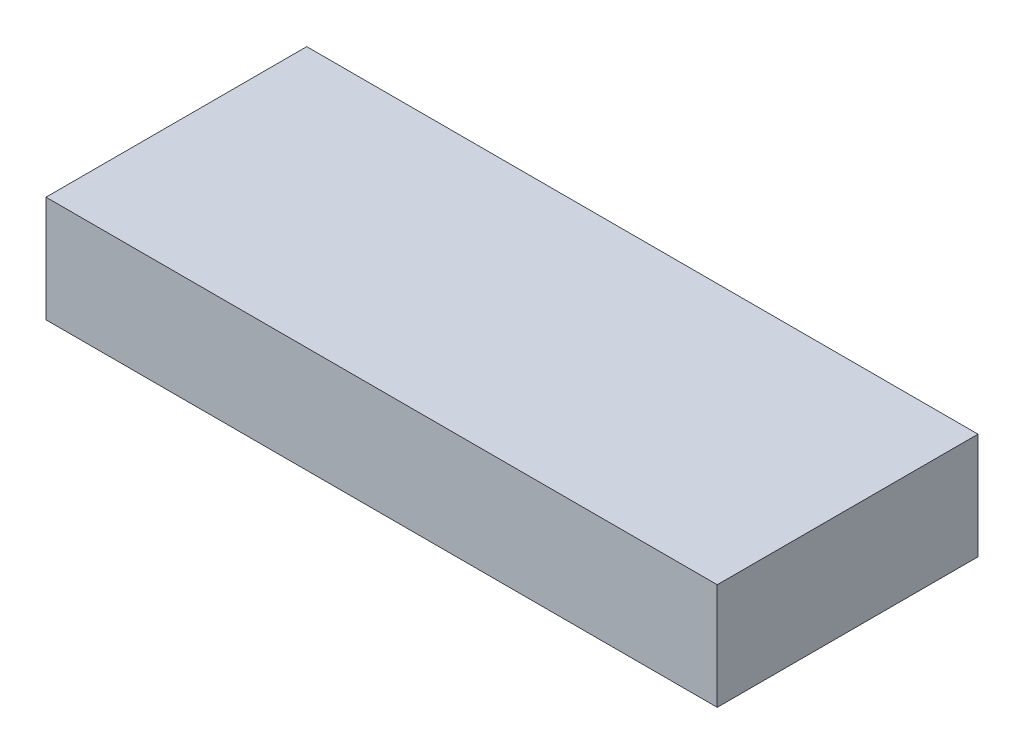
SolidWorks part; units mm, degrees
ref_plane "Front Plane" through (0, 0, 0) normal (0, 0, 1) x (1, 0, 0)
ref_plane "Top Plane" through (0, 0, 0) normal (0, 1, 0) x (1, 0, 0)
ref_plane "Right Plane" through (0, 0, 0) normal (1, 0, 0) x (0, 0, -1)
sketch "Sketch1" plane through (0, 0, 0) normal (0, 1, 0) x (1, 0, 0)
  line L1 (63.1856, 24.5456) -> (-63.1856, 24.5456)
  line L2 (63.1856, 24.5456) -> (63.1856, -24.5456)
  line L3 (63.1856, -24.5456) -> (-63.1856, -24.5456)
  line L4 (-63.1856, 24.5456) -> (-63.1856, -24.5456)
  line L5 (63.1856, 24.5456) -> (-63.1856, -24.5456) construction
  line L6 (63.1856, -24.5456) -> (-63.1856, 24.5456) construction
  point P0 (0, 0)
extrude "Boss-Extrude1" add sketch "Sketch1" along normal blind 20
ref_point "Point1" parameters "D1"=10
